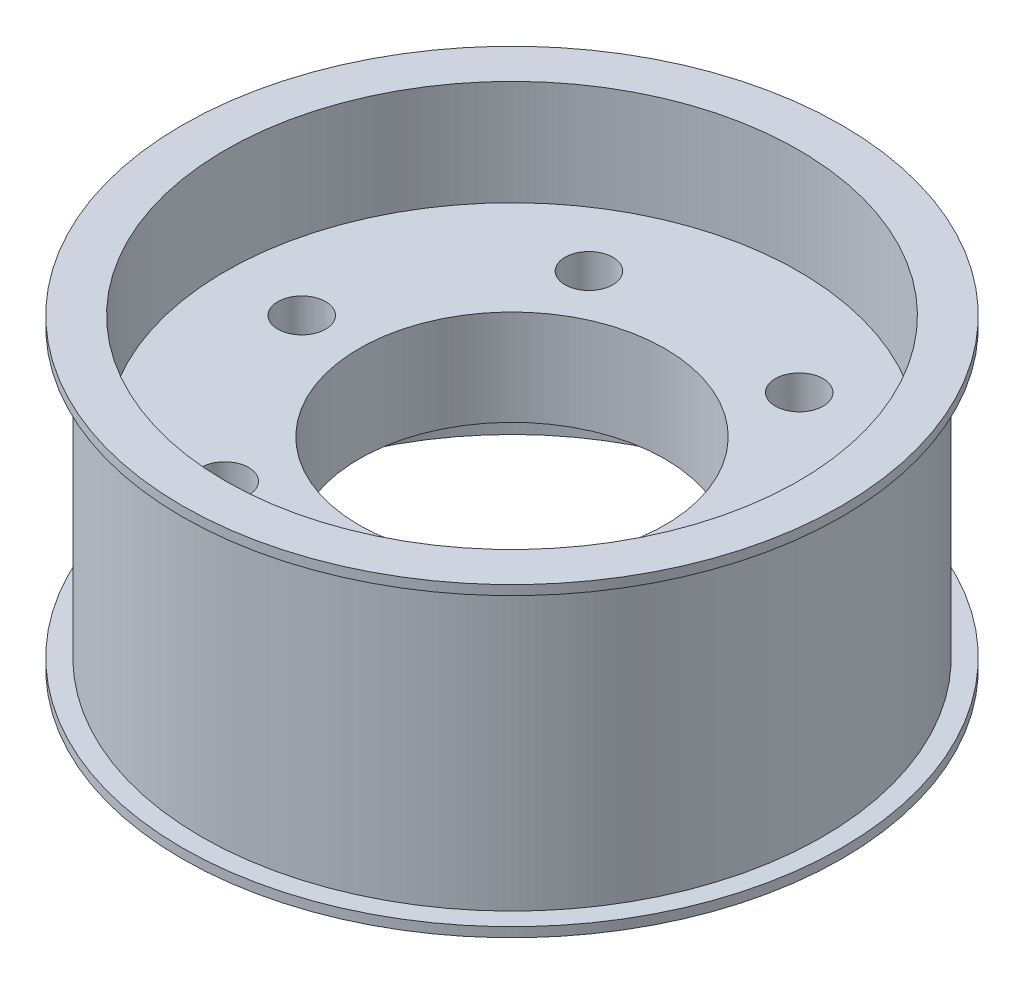
SolidWorks part; units mm, degrees
ref_plane "Front Plane" through (0, 0, 0) normal (0, 0, 1) x (1, 0, 0)
ref_plane "Top Plane" through (0, 0, 0) normal (0, 1, 0) x (1, 0, 0)
ref_plane "Right Plane" through (0, 0, 0) normal (1, 0, 0) x (0, 0, -1)
sketch "Sketch1" plane through (0, 0, 0) normal (0, 0, 1) x (1, 0, 0)
  line L0 (0, 8.983) -> (0, -8.1325) construction
  line L1 (0, 0) -> (10.9341, 0) construction
  line L2 (15, 8) -> (17.25, 8)
  line L3 (17.25, 8) -> (17.25, 7.5)
  line L4 (17.25, 7.5) -> (16.25, 7.5)
  line L5 (16.25, 7.5) -> (16.25, -7.5)
  line L6 (15, 8) -> (15, 2.5)
  line L7 (15, 2.5) -> (0, 2.5)
  line L8 (15, -2.5) -> (0, -2.5)
  line L9 (15, -8) -> (15, -2.5)
  line L10 (17.25, -7.5) -> (16.25, -7.5)
  line L11 (17.25, -8) -> (17.25, -7.5)
  line L12 (15, -8) -> (17.25, -8)
  line L13 (0, 2.5) -> (0, -2.5)
  point P13 (16.25, 0)
  dimension "D1" = 0.5
  dimension "D2" = 1
  dimension "D3" = 15
  dimension "D4" = 30
  dimension "D5" = 2.5
  dimension "34" = 32.5
revolve "Revolve1" add sketch "Sketch1" angle 360 about L0
sketch "Sketch2" plane through (0, 2.5, 0) normal (0, 1, 0) x (1, 0, 0)
  circle A0 centre (0, 0) radius 11 construction
  circle A1 centre (11, 0) radius 1.25
  circle A2 centre (5.5, -9.5263) radius 1.25
  circle A3 centre (-5.5, -9.5263) radius 1.25
  circle A4 centre (-11, 0) radius 1.25
  circle A5 centre (-5.5, 9.5263) radius 1.25
  circle A6 centre (5.5, 9.5263) radius 1.25
  circle A7 centre (0, 0) radius 8
  point P17 (0, 0)
  dimension "D1" = 22
  dimension "D2" = 2.5
  dimension "D4" = 16
  dimension "D3" = 6
extrude "Cut-Extrude1" cut sketch "Sketch2" against normal mid plane 20
